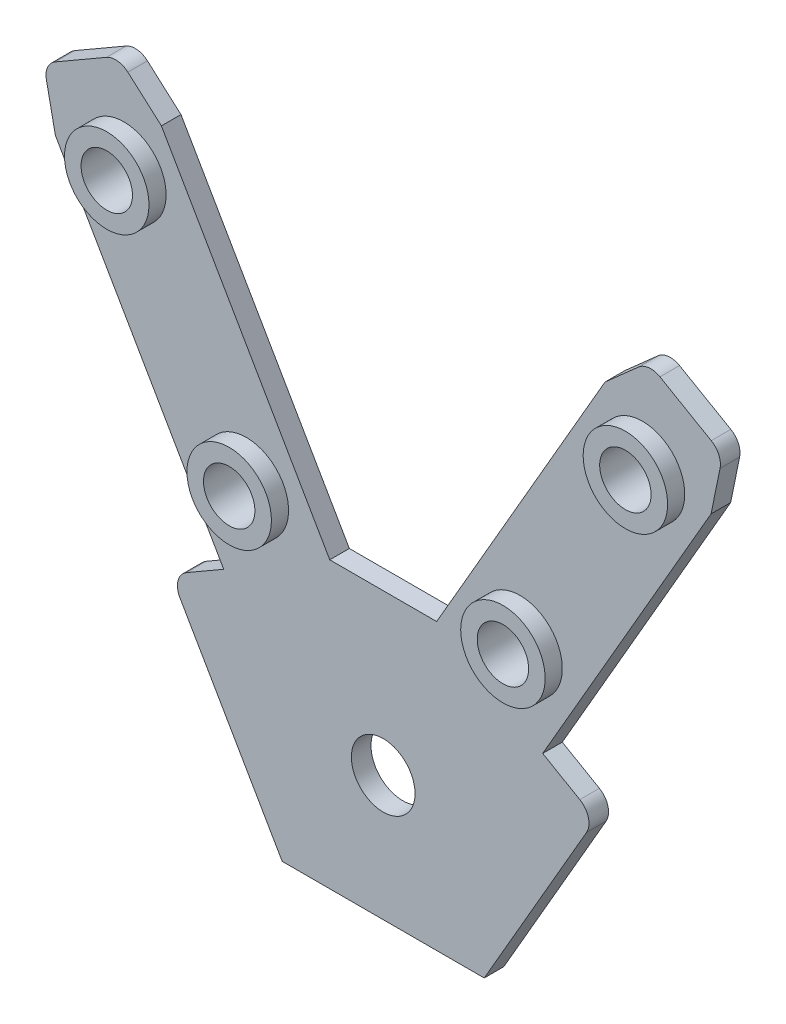
SolidWorks part; units mm, degrees
material "Plain Carbon Steel"
ref_plane "Front Plane" through (0, 0, 0) normal (0, 0, 1) x (1, 0, 0)
ref_plane "Top Plane" through (0, 0, 0) normal (0, 1, 0) x (1, 0, 0)
ref_plane "Right Plane" through (0, 0, 0) normal (1, 0, 0) x (0, 0, -1)
sketch "Sketch1" plane through (0, 0, 0) normal (0, 0, 1) x (1, 0, 0)
  line L0 (0, 0) -> (0, 67.9164) construction
  line L1 (-4.3648, 13.06) -> (4.3648, 13.06)
  line L2 (4.3648, 13.06) -> (18.1148, 36.8757)
  line L3 (18.1148, 36.8757) -> (20.8549, 39.3055)
  line L4 (22.6001, 39.4822) -> (26.7897, 37.0634)
  line L5 (24.6949, 38.2728) -> (0.6115, -3.4408) construction
  line L6 (26.775, 31.8757) -> (27.5092, 35.4636)
  line L7 (13.025, 8.06) -> (26.775, 31.8757)
  line L8 (13.025, 8.06) -> (16.0561, 6.31)
  line L9 (16.6051, 4.261) -> (8.2503, -10.21)
  line L10 (8.2503, -10.21) -> (-8.2503, -10.21)
  line L11 (-16.6051, 4.261) -> (-8.2503, -10.21)
  line L12 (-13.025, 8.06) -> (-16.0561, 6.31)
  line L13 (-13.025, 8.06) -> (-26.775, 31.8757)
  line L14 (-26.775, 31.8757) -> (-27.5092, 35.4636)
  line L15 (-22.6001, 39.4822) -> (-26.7897, 37.0634)
  line L16 (-18.1148, 36.8757) -> (-20.8549, 39.3055)
  line L17 (-4.3648, 13.06) -> (-18.1148, 36.8757)
  circle A0 centre (0, 0) radius 2.6
  arc A1 (-27.5092, 35.4636) -> (-26.7897, 37.0634) centre (-26.0397, 35.7643) cw
  arc A2 (-22.6001, 39.4822) -> (-20.8549, 39.3055) centre (-21.8501, 38.1832) cw
  arc A3 (20.8549, 39.3055) -> (22.6001, 39.4822) centre (21.8501, 38.1832) cw
  arc A4 (27.5092, 35.4636) -> (26.7897, 37.0634) centre (26.0397, 35.7643) ccw
  arc A5 (-16.6051, 4.261) -> (-16.0561, 6.31) centre (-15.3061, 5.011) cw
  arc A6 (16.0561, 6.31) -> (16.6051, 4.261) centre (15.3061, 5.011) cw
  point P17 (0, -10.21)
  point P24 (0, 13.06)
  point P26 (-27.726, 36.5228)
  point P29 (-21.6638, 40.0228)
  point P32 (21.6638, 40.0228)
  point P35 (27.726, 36.5228)
  point P38 (-17.3551, 5.56)
  point P41 (17.3551, 5.56)
  dimension "D4" = 5
  dimension "D8" = 10.21
  dimension "D9" = 2.25
  dimension "D10" = 23.27
  dimension "D11" = 1.5
  dimension "D1" = 5.2
  dimension "D2" = 10
  dimension "D3" = 30
  dimension "D5" = 32
  dimension "D6" = 4.5
  dimension "D7" = 7
extrude "Boss-Extrude1" add sketch "Sketch1" along normal blind 1.6
sketch "Sketch2" plane through (0, 0, 1.6) normal (0, 0, 1) x (1, 0, 0)
  line L0 (-24.6949, 38.2728) -> (-5.8875, 5.6975) construction
  line L1 (-22.6001, 39.4822) -> (-26.7897, 37.0634) construction
  line L2 (0, 13.06) -> (0, 26.5175) construction
  line L5 (-4.3648, 13.06) -> (-18.1148, 36.8757) construction
  line L8 (4.3648, 13.06) -> (-4.3648, 13.06) construction
  line L9 (-11.1786, 14.8618) -> (-15.5087, 12.3618) construction
  line L10 (-26.775, 31.8757) -> (-13.025, 8.06) construction
  circle A0 centre (21.1786, 32.1823) radius 3.45
  circle A1 centre (11.1786, 14.8618) radius 3.45
  circle A4 centre (-11.1786, 14.8618) radius 3.45
  circle A5 centre (-21.1786, 32.1823) radius 3.45
  dimension "D1" = 6.9
  dimension "D2" = 18.46
  dimension "D4" = 20
extrude "Boss-Extrude2" add sketch "Sketch2" along normal blind 1.4
hole_wizard "M5x0.8 Tapped Hole1" positions "Sketch4" profile "Sketch3" tap size "M5x0.8" standard "ANSI Metric" end condition through all
sketch "Sketch4" plane through (0, 0, 3) normal (0, 0, 1) x (1, 0, 0)
  point P0 (21.1786, 32.1823)
  point P3 (11.1786, 14.8618)
  point P13 (-11.1786, 14.8618)
  point P16 (-21.1786, 32.1823)
cosmetic thread "Hole Thread3" parameters "D2"=5
cosmetic thread "Hole Thread5" parameters "D2"=5
cosmetic thread "Hole Thread6" parameters "D2"=5
cosmetic thread "Hole Thread7" parameters "D2"=5
sketch "Sketch3" plane through (21.1786, 32.1823, 3) normal (1, 0, 0) x (0, -1, 0)
  line L0 (0, 0) -> (0, 3)
  line L1 (0, 3) -> (2.1, 3)
  line L2 (2.1, 3) -> (2.1, 0)
  line L5 (2.1, 0) -> (0, 0)
  line L11 (0, -6.35) -> (0, 107.95) construction
  dimension "Thru Tap Drill Dia." = 4.2
  dimension "Thru Tap Drill Depth" = 3
